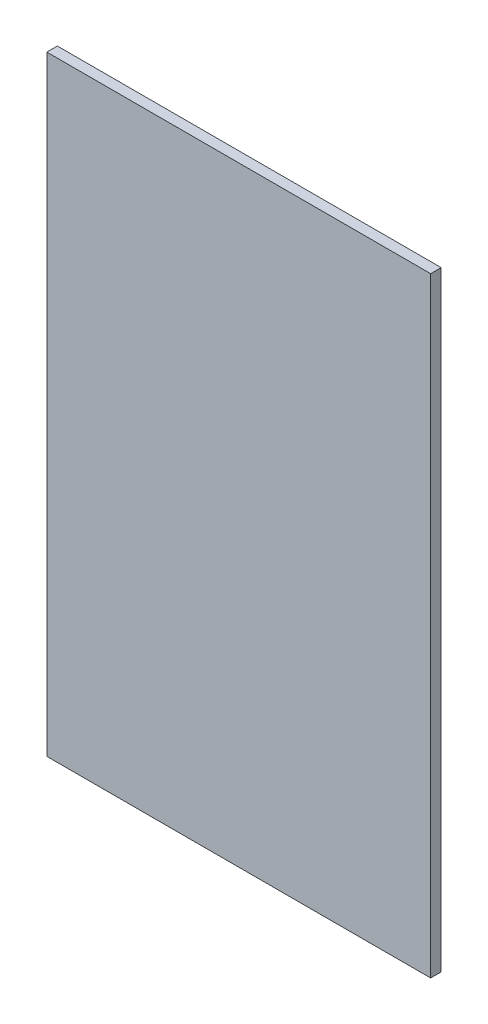
SolidWorks part; units mm, degrees
ref_plane "Plan de face" through (0, 0, 0) normal (0, 0, 1) x (1, 0, 0)
ref_plane "Plan de dessus" through (0, 0, 0) normal (0, 1, 0) x (1, 0, 0)
ref_plane "Plan de droite" through (0, 0, 0) normal (1, 0, 0) x (0, 0, -1)
sketch "Esquisse1" plane through (0, 0, 0) normal (0, 0, 1) x (1, 0, 0)
  line L1 (-108.0167, 44.5406) -> (256.9833, 44.5406)
  line L2 (-108.0167, 44.5406) -> (-108.0167, -535.4594)
  line L3 (-108.0167, -535.4594) -> (256.9833, -535.4594)
  line L4 (256.9833, 44.5406) -> (256.9833, -535.4594)
  dimension "D1" = 365
  dimension "D2" = 580
extrude "Boss.-Extru.1" add sketch "Esquisse1" along normal blind 10
equation "\"LargeurPlacard\"=160+70+135"
equation "\"D1@Esquisse1\"=\"LargeurPlacard\""
equation "\"ProfondeurPlacard\"=580"
equation "\"D2@Esquisse1\"=\"ProfondeurPlacard\""
equation "\"EpaisseurPlaque\"= 10"
equation "\"DistanceAvantSyphon\"=240"
equation "\"DistanceAvantEvier\"=100"
equation "\"DiametreTuyau\"=90"
equation "\"HauteurTuyau\"=430"
equation "\"LargeurAeration\"=260"
equation "\"HauteurAeration\"=340"
equation "\"AerationSol\"=210"
equation "\"AerationAvant\"=270"
equation "\"ProfondeurCharniere\"=80"
equation "\"HauteurCharniere\"=60"
equation "\"LargeurCharniere\"=60"
equation "\"HauteurPlacard\"=650"
equation "\"HauteurEvier\"=\"HauteurPlacard\"-555"
equation "\"HauteurDroitEvier\"=\"HauteurPlacard\" -500"
equation "\"HauteurSolSyphon\"=320"
equation "\"DiametreSyphon\"=70"
equation "\"PositionSyphonCoteGauche\"=160"
